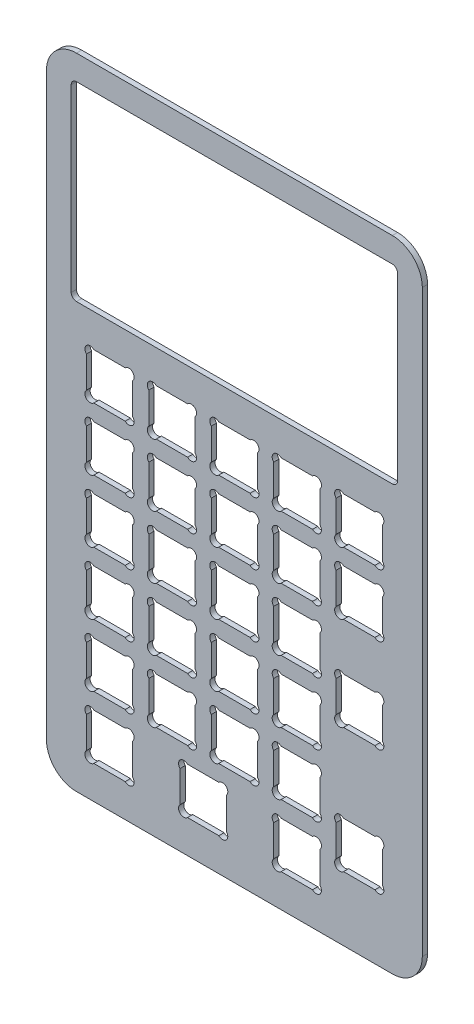
SolidWorks part; units mm, degrees
material "Brass"
ref_plane "Front Plane" through (0, 0, 0) normal (0, 0, 1) x (1, 0, 0)
ref_plane "Top Plane" through (0, 0, 0) normal (0, 1, 0) x (1, 0, 0)
ref_plane "Right Plane" through (0, 0, 0) normal (1, 0, 0) x (0, 0, -1)
sketch "Sketch1" plane through (0, 0, 0) normal (0, 0, 1) x (1, 0, 0)
  line L0 (-80.6226, 118.5954) -> (-71.1174, 118.5954)
  line L1 (0, 0) -> (-113.9, 0)
  line L2 (0, 0) -> (0, 193.7954)
  line L3 (0, 193.7954) -> (-113.9, 193.7954)
  line L4 (-113.9, 0) -> (-113.9, 193.7954)
  line L5 (-99.5426, 118.5954) -> (-90.0374, 118.5954)
  line L6 (-101.7877, 116.3503) -> (-101.7877, 106.8451)
  line L7 (-99.5426, 104.6) -> (-90.0374, 104.6)
  line L8 (-87.7923, 116.3503) -> (-87.7923, 106.8451)
  line L9 (-82.8677, 116.3503) -> (-82.8677, 106.8451)
  line L10 (-80.6226, 104.6) -> (-71.1174, 104.6)
  line L11 (-68.8723, 116.3503) -> (-68.8723, 106.8451)
  line L12 (-61.7026, 118.5954) -> (-52.1974, 118.5954)
  line L13 (-63.9477, 116.3503) -> (-63.9477, 106.8451)
  line L14 (-61.7026, 104.6) -> (-52.1974, 104.6)
  line L15 (-49.9523, 116.3503) -> (-49.9523, 106.8451)
  line L16 (-42.7826, 118.5954) -> (-33.2774, 118.5954)
  line L17 (-45.0277, 116.3503) -> (-45.0277, 106.8451)
  line L18 (-42.7826, 104.6) -> (-33.2774, 104.6)
  line L19 (-31.0323, 116.3503) -> (-31.0323, 106.8451)
  line L20 (-23.8626, 118.5954) -> (-14.3574, 118.5954)
  line L21 (-26.1077, 116.3503) -> (-26.1077, 106.8451)
  line L22 (-23.8626, 104.6) -> (-14.3574, 104.6)
  line L23 (-12.1123, 116.3503) -> (-12.1123, 106.8451)
  line L24 (-80.6226, 99.6754) -> (-71.1174, 99.6754)
  line L25 (-82.8677, 97.4303) -> (-82.8677, 87.9251)
  line L26 (-80.6226, 85.68) -> (-71.1174, 85.68)
  line L27 (-68.8723, 97.4303) -> (-68.8723, 87.9251)
  line L28 (-61.7026, 99.6754) -> (-52.1974, 99.6754)
  line L29 (-63.9477, 97.4303) -> (-63.9477, 87.9251)
  line L30 (-61.7026, 85.68) -> (-52.1974, 85.68)
  line L31 (-49.9523, 97.4303) -> (-49.9523, 87.9251)
  line L32 (-42.7826, 99.6754) -> (-33.2774, 99.6754)
  line L33 (-45.0277, 97.4303) -> (-45.0277, 87.9251)
  line L34 (-42.7826, 85.68) -> (-33.2774, 85.68)
  line L35 (-31.0323, 97.4303) -> (-31.0323, 87.9251)
  line L36 (-23.8626, 99.6754) -> (-14.3574, 99.6754)
  line L37 (-26.1077, 97.4303) -> (-26.1077, 87.9251)
  line L38 (-23.8626, 85.68) -> (-14.3574, 85.68)
  line L39 (-12.1123, 97.4303) -> (-12.1123, 87.9251)
  line L40 (-80.6226, 80.7554) -> (-71.1174, 80.7554)
  line L41 (-82.8677, 78.5103) -> (-82.8677, 69.0051)
  line L42 (-80.6226, 66.76) -> (-71.1174, 66.76)
  line L43 (-68.8723, 78.5103) -> (-68.8723, 69.0051)
  line L44 (-61.7026, 80.7554) -> (-52.1974, 80.7554)
  line L45 (-63.9477, 78.5103) -> (-63.9477, 69.0051)
  line L46 (-61.7026, 66.76) -> (-52.1974, 66.76)
  line L47 (-49.9523, 78.5103) -> (-49.9523, 69.0051)
  line L48 (-42.7826, 80.7554) -> (-33.2774, 80.7554)
  line L49 (-45.0277, 78.5103) -> (-45.0277, 69.0051)
  line L50 (-42.7826, 66.76) -> (-33.2774, 66.76)
  line L51 (-31.0323, 78.5103) -> (-31.0323, 69.0051)
  line L56 (-80.6226, 61.8354) -> (-71.1174, 61.8354)
  line L57 (-82.8677, 59.5903) -> (-82.8677, 50.0851)
  line L58 (-80.6226, 47.84) -> (-71.1174, 47.84)
  line L59 (-68.8723, 59.5903) -> (-68.8723, 50.0851)
  line L60 (-61.7026, 61.8354) -> (-52.1974, 61.8354)
  line L61 (-63.9477, 59.5903) -> (-63.9477, 50.0851)
  line L62 (-61.7026, 47.84) -> (-52.1974, 47.84)
  line L63 (-49.9523, 59.5903) -> (-49.9523, 50.0851)
  line L64 (-42.7826, 61.8354) -> (-33.2774, 61.8354)
  line L65 (-45.0277, 59.5903) -> (-45.0277, 50.0851)
  line L66 (-42.7826, 47.84) -> (-33.2774, 47.84)
  line L67 (-31.0323, 59.5903) -> (-31.0323, 50.0851)
  line L72 (-80.6226, 42.9154) -> (-71.1174, 42.9154)
  line L73 (-82.8677, 40.6703) -> (-82.8677, 31.1651)
  line L74 (-80.6226, 28.92) -> (-71.1174, 28.92)
  line L75 (-68.8723, 40.6703) -> (-68.8723, 31.1651)
  line L76 (-61.7026, 42.9154) -> (-52.1974, 42.9154)
  line L77 (-63.9477, 40.6703) -> (-63.9477, 31.1651)
  line L78 (-61.7026, 28.92) -> (-52.1974, 28.92)
  line L79 (-49.9523, 40.6703) -> (-49.9523, 31.1651)
  line L80 (-42.7826, 42.9154) -> (-33.2774, 42.9154)
  line L81 (-45.0277, 40.6703) -> (-45.0277, 31.1651)
  line L82 (-42.7826, 28.92) -> (-33.2774, 28.92)
  line L83 (-31.0323, 40.6703) -> (-31.0323, 31.1651)
  line L96 (-42.7826, 23.9954) -> (-33.2774, 23.9954)
  line L97 (-45.0277, 21.7503) -> (-45.0277, 12.2451)
  line L98 (-42.7826, 10) -> (-33.2774, 10)
  line L99 (-31.0323, 21.7503) -> (-31.0323, 12.2451)
  line L104 (-99.5426, 99.6754) -> (-90.0374, 99.6754)
  line L105 (-101.7877, 97.4303) -> (-101.7877, 87.9251)
  line L106 (-99.5426, 85.68) -> (-90.0374, 85.68)
  line L107 (-87.7923, 97.4303) -> (-87.7923, 87.9251)
  line L108 (-99.5426, 80.7554) -> (-90.0374, 80.7554)
  line L109 (-101.7877, 78.5103) -> (-101.7877, 69.0051)
  line L110 (-99.5426, 66.76) -> (-90.0374, 66.76)
  line L111 (-87.7923, 78.5103) -> (-87.7923, 69.0051)
  line L112 (-99.5426, 61.8354) -> (-90.0374, 61.8354)
  line L113 (-101.7877, 59.5903) -> (-101.7877, 50.0851)
  line L114 (-99.5426, 47.84) -> (-90.0374, 47.84)
  line L115 (-87.7923, 59.5903) -> (-87.7923, 50.0851)
  line L116 (-99.5426, 42.9154) -> (-90.0374, 42.9154)
  line L117 (-101.7877, 40.6703) -> (-101.7877, 31.1651)
  line L118 (-99.5426, 28.92) -> (-90.0374, 28.92)
  line L119 (-87.7923, 40.6703) -> (-87.7923, 31.1651)
  line L120 (-99.5426, 23.9954) -> (-90.0374, 23.9954)
  line L121 (-101.7877, 21.7503) -> (-101.7877, 12.2451)
  line L122 (-99.5426, 10) -> (-90.0374, 10)
  line L123 (-87.7923, 21.7503) -> (-87.7923, 12.2451)
  line L124 (-23.8626, 80.7554) -> (-14.3574, 80.7554) [skipped]
  line L125 (-26.1077, 78.5103) -> (-26.1077, 69.0051) [skipped]
  line L126 (-23.8626, 66.76) -> (-14.3574, 66.76) [skipped]
  line L127 (-12.1123, 78.5103) -> (-12.1123, 69.0051) [skipped]
  line L128 (-23.8626, 61.8354) -> (-14.3574, 61.8354) [skipped]
  line L129 (-26.1077, 59.5903) -> (-26.1077, 50.0851) [skipped]
  line L130 (-23.8626, 47.84) -> (-14.3574, 47.84) [skipped]
  line L131 (-12.1123, 59.5903) -> (-12.1123, 50.0851) [skipped]
  line L132 (-23.8626, 42.9154) -> (-14.3574, 42.9154) [skipped]
  line L133 (-26.1077, 40.6703) -> (-26.1077, 31.1651) [skipped]
  line L134 (-23.8626, 28.92) -> (-14.3574, 28.92) [skipped]
  line L135 (-12.1123, 40.6703) -> (-12.1123, 31.1651) [skipped]
  line L136 (-23.8626, 23.9954) -> (-14.3574, 23.9954) [skipped]
  line L137 (-26.1077, 21.7503) -> (-26.1077, 12.2451) [skipped]
  line L138 (-23.8626, 10) -> (-14.3574, 10) [skipped]
  line L139 (-12.1123, 21.7503) -> (-12.1123, 12.2451) [skipped]
  line L140 (-80.6226, 23.9954) -> (-71.1174, 23.9954) [skipped]
  line L141 (-82.8677, 21.7503) -> (-82.8677, 12.2451) [skipped]
  line L142 (-80.6226, 10) -> (-71.1174, 10) [skipped]
  line L143 (-68.8723, 21.7503) -> (-68.8723, 12.2451) [skipped]
  line L144 (-61.7026, 23.9954) -> (-52.1974, 23.9954) [skipped]
  line L145 (-63.9477, 21.7503) -> (-63.9477, 12.2451) [skipped]
  line L146 (-61.7026, 10) -> (-52.1974, 10) [skipped]
  line L147 (-49.9523, 21.7503) -> (-49.9523, 12.2451) [skipped]
  line L148 (-68.8723, 31.1651) -> (-63.9477, 31.1651) construction
  line L149 (-71.1626, 23.9954) -> (-61.6574, 23.9954)
  line L150 (-73.4077, 21.7503) -> (-73.4077, 12.2451)
  line L151 (-71.1626, 10) -> (-61.6574, 10)
  line L152 (-59.4123, 21.7503) -> (-59.4123, 12.2451)
  line L153 (-23.8626, 33.4554) -> (-14.3574, 33.4554)
  line L154 (-26.1077, 31.2103) -> (-26.1077, 21.7051)
  line L155 (-23.8626, 19.46) -> (-14.3574, 19.46)
  line L156 (-12.1123, 31.2103) -> (-12.1123, 21.7051)
  line L157 (-23.8626, 71.2954) -> (-14.3574, 71.2954)
  line L158 (-26.1077, 69.0503) -> (-26.1077, 59.5451)
  line L159 (-23.8626, 57.3) -> (-14.3574, 57.3)
  line L160 (-12.1123, 69.0503) -> (-12.1123, 59.5451)
  line L161 (-33.2774, 28.92) -> (-33.2774, 23.9954) construction
  line L162 (-33.2774, 66.76) -> (-33.2774, 61.8354) construction
  line L163 (-56.95, 193.7954) -> (-56.95, 0) construction
  line L164 (-104.8125, 186.2954) -> (-9.0875, 186.2954)
  line L165 (-106.4, 184.7079) -> (-106.4, 130.1829)
  line L166 (-104.8125, 128.5954) -> (-9.0875, 128.5954)
  line L167 (-7.5, 184.7079) -> (-7.5, 130.1829)
  arc A4 (-99.5426, 118.5954) -> (-101.7877, 116.3503) centre (-100.6652, 117.4729) ccw
  arc A5 (-101.7877, 106.8451) -> (-99.5426, 104.6) centre (-100.6652, 105.7225) ccw
  arc A6 (-90.0374, 104.6) -> (-87.7923, 106.8451) centre (-88.9148, 105.7225) ccw
  arc A7 (-87.7923, 116.3503) -> (-90.0374, 118.5954) centre (-88.9148, 117.4729) ccw
  arc A8 (-80.6226, 118.5954) -> (-82.8677, 116.3503) centre (-81.7452, 117.4729) ccw
  arc A9 (-82.8677, 106.8451) -> (-80.6226, 104.6) centre (-81.7452, 105.7225) ccw
  arc A10 (-71.1174, 104.6) -> (-68.8723, 106.8451) centre (-69.9948, 105.7225) ccw
  arc A11 (-68.8723, 116.3503) -> (-71.1174, 118.5954) centre (-69.9948, 117.4729) ccw
  arc A12 (-61.7026, 118.5954) -> (-63.9477, 116.3503) centre (-62.8252, 117.4729) ccw
  arc A13 (-63.9477, 106.8451) -> (-61.7026, 104.6) centre (-62.8252, 105.7225) ccw
  arc A14 (-52.1974, 104.6) -> (-49.9523, 106.8451) centre (-51.0748, 105.7225) ccw
  arc A15 (-49.9523, 116.3503) -> (-52.1974, 118.5954) centre (-51.0748, 117.4729) ccw
  arc A16 (-42.7826, 118.5954) -> (-45.0277, 116.3503) centre (-43.9052, 117.4729) ccw
  arc A17 (-45.0277, 106.8451) -> (-42.7826, 104.6) centre (-43.9052, 105.7225) ccw
  arc A18 (-33.2774, 104.6) -> (-31.0323, 106.8451) centre (-32.1548, 105.7225) ccw
  arc A19 (-31.0323, 116.3503) -> (-33.2774, 118.5954) centre (-32.1548, 117.4729) ccw
  arc A20 (-23.8626, 118.5954) -> (-26.1077, 116.3503) centre (-24.9852, 117.4729) ccw
  arc A21 (-26.1077, 106.8451) -> (-23.8626, 104.6) centre (-24.9852, 105.7225) ccw
  arc A22 (-14.3574, 104.6) -> (-12.1123, 106.8451) centre (-13.2348, 105.7225) ccw
  arc A23 (-12.1123, 116.3503) -> (-14.3574, 118.5954) centre (-13.2348, 117.4729) ccw
  arc A24 (-80.6226, 99.6754) -> (-82.8677, 97.4303) centre (-81.7452, 98.5529) ccw
  arc A25 (-82.8677, 87.9251) -> (-80.6226, 85.68) centre (-81.7452, 86.8025) ccw
  arc A26 (-71.1174, 85.68) -> (-68.8723, 87.9251) centre (-69.9948, 86.8025) ccw
  arc A27 (-68.8723, 97.4303) -> (-71.1174, 99.6754) centre (-69.9948, 98.5529) ccw
  arc A28 (-61.7026, 99.6754) -> (-63.9477, 97.4303) centre (-62.8252, 98.5529) ccw
  arc A29 (-63.9477, 87.9251) -> (-61.7026, 85.68) centre (-62.8252, 86.8025) ccw
  arc A30 (-52.1974, 85.68) -> (-49.9523, 87.9251) centre (-51.0748, 86.8025) ccw
  arc A31 (-49.9523, 97.4303) -> (-52.1974, 99.6754) centre (-51.0748, 98.5529) ccw
  arc A32 (-42.7826, 99.6754) -> (-45.0277, 97.4303) centre (-43.9052, 98.5529) ccw
  arc A33 (-45.0277, 87.9251) -> (-42.7826, 85.68) centre (-43.9052, 86.8025) ccw
  arc A34 (-33.2774, 85.68) -> (-31.0323, 87.9251) centre (-32.1548, 86.8025) ccw
  arc A35 (-31.0323, 97.4303) -> (-33.2774, 99.6754) centre (-32.1548, 98.5529) ccw
  arc A36 (-23.8626, 99.6754) -> (-26.1077, 97.4303) centre (-24.9852, 98.5529) ccw
  arc A37 (-26.1077, 87.9251) -> (-23.8626, 85.68) centre (-24.9852, 86.8025) ccw
  arc A38 (-14.3574, 85.68) -> (-12.1123, 87.9251) centre (-13.2348, 86.8025) ccw
  arc A39 (-12.1123, 97.4303) -> (-14.3574, 99.6754) centre (-13.2348, 98.5529) ccw
  arc A40 (-80.6226, 80.7554) -> (-82.8677, 78.5103) centre (-81.7452, 79.6329) ccw
  arc A41 (-82.8677, 69.0051) -> (-80.6226, 66.76) centre (-81.7452, 67.8825) ccw
  arc A42 (-71.1174, 66.76) -> (-68.8723, 69.0051) centre (-69.9948, 67.8825) ccw
  arc A43 (-68.8723, 78.5103) -> (-71.1174, 80.7554) centre (-69.9948, 79.6329) ccw
  arc A44 (-61.7026, 80.7554) -> (-63.9477, 78.5103) centre (-62.8252, 79.6329) ccw
  arc A45 (-63.9477, 69.0051) -> (-61.7026, 66.76) centre (-62.8252, 67.8825) ccw
  arc A46 (-52.1974, 66.76) -> (-49.9523, 69.0051) centre (-51.0748, 67.8825) ccw
  arc A47 (-49.9523, 78.5103) -> (-52.1974, 80.7554) centre (-51.0748, 79.6329) ccw
  arc A48 (-42.7826, 80.7554) -> (-45.0277, 78.5103) centre (-43.9052, 79.6329) ccw
  arc A49 (-45.0277, 69.0051) -> (-42.7826, 66.76) centre (-43.9052, 67.8825) ccw
  arc A50 (-33.2774, 66.76) -> (-31.0323, 69.0051) centre (-32.1548, 67.8825) ccw
  arc A51 (-31.0323, 78.5103) -> (-33.2774, 80.7554) centre (-32.1548, 79.6329) ccw
  arc A56 (-80.6226, 61.8354) -> (-82.8677, 59.5903) centre (-81.7452, 60.7129) ccw
  arc A57 (-82.8677, 50.0851) -> (-80.6226, 47.84) centre (-81.7452, 48.9625) ccw
  arc A58 (-71.1174, 47.84) -> (-68.8723, 50.0851) centre (-69.9948, 48.9625) ccw
  arc A59 (-68.8723, 59.5903) -> (-71.1174, 61.8354) centre (-69.9948, 60.7129) ccw
  arc A60 (-61.7026, 61.8354) -> (-63.9477, 59.5903) centre (-62.8252, 60.7129) ccw
  arc A61 (-63.9477, 50.0851) -> (-61.7026, 47.84) centre (-62.8252, 48.9625) ccw
  arc A62 (-52.1974, 47.84) -> (-49.9523, 50.0851) centre (-51.0748, 48.9625) ccw
  arc A63 (-49.9523, 59.5903) -> (-52.1974, 61.8354) centre (-51.0748, 60.7129) ccw
  arc A64 (-42.7826, 61.8354) -> (-45.0277, 59.5903) centre (-43.9052, 60.7129) ccw
  arc A65 (-45.0277, 50.0851) -> (-42.7826, 47.84) centre (-43.9052, 48.9625) ccw
  arc A66 (-33.2774, 47.84) -> (-31.0323, 50.0851) centre (-32.1548, 48.9625) ccw
  arc A67 (-31.0323, 59.5903) -> (-33.2774, 61.8354) centre (-32.1548, 60.7129) ccw
  arc A72 (-80.6226, 42.9154) -> (-82.8677, 40.6703) centre (-81.7452, 41.7929) ccw
  arc A73 (-82.8677, 31.1651) -> (-80.6226, 28.92) centre (-81.7452, 30.0425) ccw
  arc A74 (-71.1174, 28.92) -> (-68.8723, 31.1651) centre (-69.9948, 30.0425) ccw
  arc A75 (-68.8723, 40.6703) -> (-71.1174, 42.9154) centre (-69.9948, 41.7929) ccw
  arc A76 (-61.7026, 42.9154) -> (-63.9477, 40.6703) centre (-62.8252, 41.7929) ccw
  arc A77 (-63.9477, 31.1651) -> (-61.7026, 28.92) centre (-62.8252, 30.0425) ccw
  arc A78 (-52.1974, 28.92) -> (-49.9523, 31.1651) centre (-51.0748, 30.0425) ccw
  arc A79 (-49.9523, 40.6703) -> (-52.1974, 42.9154) centre (-51.0748, 41.7929) ccw
  arc A80 (-42.7826, 42.9154) -> (-45.0277, 40.6703) centre (-43.9052, 41.7929) ccw
  arc A81 (-45.0277, 31.1651) -> (-42.7826, 28.92) centre (-43.9052, 30.0425) ccw
  arc A82 (-33.2774, 28.92) -> (-31.0323, 31.1651) centre (-32.1548, 30.0425) ccw
  arc A83 (-31.0323, 40.6703) -> (-33.2774, 42.9154) centre (-32.1548, 41.7929) ccw
  arc A96 (-42.7826, 23.9954) -> (-45.0277, 21.7503) centre (-43.9052, 22.8729) ccw
  arc A97 (-45.0277, 12.2451) -> (-42.7826, 10) centre (-43.9052, 11.1225) ccw
  arc A98 (-33.2774, 10) -> (-31.0323, 12.2451) centre (-32.1548, 11.1225) ccw
  arc A99 (-31.0323, 21.7503) -> (-33.2774, 23.9954) centre (-32.1548, 22.8729) ccw
  arc A104 (-99.5426, 99.6754) -> (-101.7877, 97.4303) centre (-100.6652, 98.5529) ccw
  arc A105 (-101.7877, 87.9251) -> (-99.5426, 85.68) centre (-100.6652, 86.8025) ccw
  arc A106 (-90.0374, 85.68) -> (-87.7923, 87.9251) centre (-88.9148, 86.8025) ccw
  arc A107 (-87.7923, 97.4303) -> (-90.0374, 99.6754) centre (-88.9148, 98.5529) ccw
  arc A108 (-99.5426, 80.7554) -> (-101.7877, 78.5103) centre (-100.6652, 79.6329) ccw
  arc A109 (-101.7877, 69.0051) -> (-99.5426, 66.76) centre (-100.6652, 67.8825) ccw
  arc A110 (-90.0374, 66.76) -> (-87.7923, 69.0051) centre (-88.9148, 67.8825) ccw
  arc A111 (-87.7923, 78.5103) -> (-90.0374, 80.7554) centre (-88.9148, 79.6329) ccw
  arc A112 (-99.5426, 61.8354) -> (-101.7877, 59.5903) centre (-100.6652, 60.7129) ccw
  arc A113 (-101.7877, 50.0851) -> (-99.5426, 47.84) centre (-100.6652, 48.9625) ccw
  arc A114 (-90.0374, 47.84) -> (-87.7923, 50.0851) centre (-88.9148, 48.9625) ccw
  arc A115 (-87.7923, 59.5903) -> (-90.0374, 61.8354) centre (-88.9148, 60.7129) ccw
  arc A116 (-99.5426, 42.9154) -> (-101.7877, 40.6703) centre (-100.6652, 41.7929) ccw
  arc A117 (-101.7877, 31.1651) -> (-99.5426, 28.92) centre (-100.6652, 30.0425) ccw
  arc A118 (-90.0374, 28.92) -> (-87.7923, 31.1651) centre (-88.9148, 30.0425) ccw
  arc A119 (-87.7923, 40.6703) -> (-90.0374, 42.9154) centre (-88.9148, 41.7929) ccw
  arc A120 (-99.5426, 23.9954) -> (-101.7877, 21.7503) centre (-100.6652, 22.8729) ccw
  arc A121 (-101.7877, 12.2451) -> (-99.5426, 10) centre (-100.6652, 11.1225) ccw
  arc A122 (-90.0374, 10) -> (-87.7923, 12.2451) centre (-88.9148, 11.1225) ccw
  arc A123 (-87.7923, 21.7503) -> (-90.0374, 23.9954) centre (-88.9148, 22.8729) ccw
  arc A124 (-23.8626, 80.7554) -> (-26.1077, 78.5103) centre (-24.9852, 79.6329) ccw [skipped]
  arc A125 (-26.1077, 69.0051) -> (-23.8626, 66.76) centre (-24.9852, 67.8825) ccw [skipped]
  arc A126 (-14.3574, 66.76) -> (-12.1123, 69.0051) centre (-13.2348, 67.8825) ccw [skipped]
  arc A127 (-12.1123, 78.5103) -> (-14.3574, 80.7554) centre (-13.2348, 79.6329) ccw [skipped]
  arc A128 (-23.8626, 61.8354) -> (-26.1077, 59.5903) centre (-24.9852, 60.7129) ccw [skipped]
  arc A129 (-26.1077, 50.0851) -> (-23.8626, 47.84) centre (-24.9852, 48.9625) ccw [skipped]
  arc A130 (-14.3574, 47.84) -> (-12.1123, 50.0851) centre (-13.2348, 48.9625) ccw [skipped]
  arc A131 (-12.1123, 59.5903) -> (-14.3574, 61.8354) centre (-13.2348, 60.7129) ccw [skipped]
  arc A132 (-23.8626, 42.9154) -> (-26.1077, 40.6703) centre (-24.9852, 41.7929) ccw [skipped]
  arc A133 (-26.1077, 31.1651) -> (-23.8626, 28.92) centre (-24.9852, 30.0425) ccw [skipped]
  arc A134 (-14.3574, 28.92) -> (-12.1123, 31.1651) centre (-13.2348, 30.0425) ccw [skipped]
  arc A135 (-12.1123, 40.6703) -> (-14.3574, 42.9154) centre (-13.2348, 41.7929) ccw [skipped]
  arc A136 (-23.8626, 23.9954) -> (-26.1077, 21.7503) centre (-24.9852, 22.8729) ccw [skipped]
  arc A137 (-26.1077, 12.2451) -> (-23.8626, 10) centre (-24.9852, 11.1225) ccw [skipped]
  arc A138 (-14.3574, 10) -> (-12.1123, 12.2451) centre (-13.2348, 11.1225) ccw [skipped]
  arc A139 (-12.1123, 21.7503) -> (-14.3574, 23.9954) centre (-13.2348, 22.8729) ccw [skipped]
  arc A140 (-80.6226, 23.9954) -> (-82.8677, 21.7503) centre (-81.7452, 22.8729) ccw [skipped]
  arc A141 (-82.8677, 12.2451) -> (-80.6226, 10) centre (-81.7452, 11.1225) ccw [skipped]
  arc A142 (-71.1174, 10) -> (-68.8723, 12.2451) centre (-69.9948, 11.1225) ccw [skipped]
  arc A143 (-68.8723, 21.7503) -> (-71.1174, 23.9954) centre (-69.9948, 22.8729) ccw [skipped]
  arc A144 (-61.7026, 23.9954) -> (-63.9477, 21.7503) centre (-62.8252, 22.8729) ccw [skipped]
  arc A145 (-63.9477, 12.2451) -> (-61.7026, 10) centre (-62.8252, 11.1225) ccw [skipped]
  arc A146 (-52.1974, 10) -> (-49.9523, 12.2451) centre (-51.0748, 11.1225) ccw [skipped]
  arc A147 (-49.9523, 21.7503) -> (-52.1974, 23.9954) centre (-51.0748, 22.8729) ccw [skipped]
  arc A148 (-71.1626, 23.9954) -> (-73.4077, 21.7503) centre (-72.2852, 22.8729) ccw
  arc A149 (-73.4077, 12.2451) -> (-71.1626, 10) centre (-72.2852, 11.1225) ccw
  arc A150 (-61.6574, 10) -> (-59.4123, 12.2451) centre (-60.5348, 11.1225) ccw
  arc A151 (-59.4123, 21.7503) -> (-61.6574, 23.9954) centre (-60.5348, 22.8729) ccw
  arc A152 (-23.8626, 33.4554) -> (-26.1077, 31.2103) centre (-24.9852, 32.3329) ccw
  arc A153 (-26.1077, 21.7051) -> (-23.8626, 19.46) centre (-24.9852, 20.5825) ccw
  arc A154 (-14.3574, 19.46) -> (-12.1123, 21.7051) centre (-13.2348, 20.5825) ccw
  arc A155 (-12.1123, 31.2103) -> (-14.3574, 33.4554) centre (-13.2348, 32.3329) ccw
  arc A156 (-23.8626, 71.2954) -> (-26.1077, 69.0503) centre (-24.9852, 70.1729) ccw
  arc A157 (-26.1077, 59.5451) -> (-23.8626, 57.3) centre (-24.9852, 58.4225) ccw
  arc A158 (-14.3574, 57.3) -> (-12.1123, 59.5451) centre (-13.2348, 58.4225) ccw
  arc A159 (-12.1123, 69.0503) -> (-14.3574, 71.2954) centre (-13.2348, 70.1729) ccw
  arc A160 (-9.0875, 186.2954) -> (-7.5, 184.7079) centre (-9.0875, 184.7079) cw
  arc A161 (-9.0875, 128.5954) -> (-7.5, 130.1829) centre (-9.0875, 130.1829) ccw
  arc A162 (-106.4, 130.1829) -> (-104.8125, 128.5954) centre (-104.8125, 130.1829) ccw
  arc A163 (-104.8125, 186.2954) -> (-106.4, 184.7079) centre (-104.8125, 184.7079) ccw
  point P8 (-101.7877, 118.5954)
  point P16 (-87.7923, 118.5954)
  point P25 (-101.7877, 104.6)
  point P27 (-87.7923, 104.6)
  point P32 (-26.1077, 26.4577)
  point P155 (-33.2774, 26.4577)
  point P159 (-73.4077, 23.9954)
  point P191 (-56.95, 186.2954)
  point P203 (-59.4123, 23.9954)
  point P206 (-73.4077, 10)
  point P207 (-59.4123, 10)
  point P210 (-66.41, 23.9954)
  point P211 (-66.41, 31.1651)
  point P251 (-26.1077, 33.4554)
  point P259 (-12.1123, 33.4554)
  point P262 (-26.1077, 19.46)
  point P263 (-12.1123, 19.46)
  point P267 (-26.1077, 71.2954)
  point P275 (-12.1123, 71.2954)
  point P278 (-26.1077, 57.3)
  point P282 (-33.2774, 64.2977)
  point P283 (-26.1077, 64.2977)
  point P284 (-7.5, 186.2954)
  point P300 (-7.5, 128.5954)
  point P302 (-56.95, 118.5954)
  point P303 (-56.95, 193.7954)
  point P309 (-106.4, 186.2954)
  point P493 (0, 0)
  dimension "D2" = 1.5875
  dimension "D11" = 7.5
  dimension "D12" = 10
  dimension "D13" = 1.5875
  dimension "D1" = 13.9954
  dimension "D3" = 10
  dimension "D4" = 113.9
  dimension "D5" = 98.9
  dimension "D6" = 57.7
  dimension "D9" = 18.92
  dimension "D10" = 18.92
  dimension "D7" = 5
  dimension "D8" = 6
extrude "Boss-Extrude1" add sketch "Sketch1" along normal blind 1.5875
fillet "Fillet1" radius 9.0875 4 edges at (-113.9, 0, 0.7937) (0, 0, 0.7937) (0, 193.7954, 0.7937) (-113.9, 193.7954, 0.7937)
sketch "Sketch2" plane through (0, 0, 1.5875) normal (0, 0, 1) x (1, 0, 0)
  line L0 (-56.9104, 20.4879) -> (-59.4123, 20.4879)
  line L1 (-73.4077, 13.6456) -> (-72.8578, 13.6456)
  line L2 (-73.4077, 21.7503) -> (-73.4077, 12.2451) construction
  line L3 (-72.8578, 13.6456) -> (-72.8578, 12.3923)
  line L4 (-72.8578, 12.3923) -> (-75.7239, 12.3923)
  line L5 (-75.7239, 12.3923) -> (-75.7239, 10.0423)
  line L6 (-75.7239, 10.0423) -> (-78.7719, 10.0423)
  line L7 (-78.7719, 10.0423) -> (-78.7719, 12.3923)
  line L8 (-78.7719, 12.3923) -> (-82.5644, 12.3923)
  line L9 (-82.5644, 12.3923) -> (-82.5644, 17.4839)
  line L10 (-82.5644, 17.4839) -> (-81.5136, 17.4839)
  line L11 (-81.5136, 17.4839) -> (-81.5136, 20.813)
  line L12 (-81.5136, 20.813) -> (-82.5644, 20.813)
  line L13 (-82.5644, 20.813) -> (-82.5644, 21.3007)
  line L14 (-82.5644, 21.3007) -> (-75.9096, 21.3007)
  line L15 (-75.9096, 21.3007) -> (-75.9096, 20.4879)
  line L16 (-75.9096, 20.4879) -> (-73.4077, 20.4879)
  line L17 (-66.41, 23.9954) -> (-66.41, 10) construction
  line L18 (-61.6574, 23.9954) -> (-71.1626, 23.9954) construction
  line L19 (-71.1626, 10) -> (-61.6574, 10) construction
  line L20 (-56.9104, 21.3007) -> (-56.9104, 20.4879)
  line L21 (-50.2556, 21.3007) -> (-56.9104, 21.3007)
  line L22 (-50.2556, 20.813) -> (-50.2556, 21.3007)
  line L23 (-51.3064, 20.813) -> (-50.2556, 20.813)
  line L24 (-51.3064, 17.4839) -> (-51.3064, 20.813)
  line L25 (-50.2556, 17.4839) -> (-51.3064, 17.4839)
  line L26 (-50.2556, 12.3923) -> (-50.2556, 17.4839)
  line L27 (-54.0481, 12.3923) -> (-50.2556, 12.3923)
  line L28 (-54.0481, 10.0423) -> (-54.0481, 12.3923)
  line L29 (-57.0961, 10.0423) -> (-54.0481, 10.0423)
  line L30 (-57.0961, 12.3923) -> (-57.0961, 10.0423)
  line L31 (-59.9622, 12.3923) -> (-57.0961, 12.3923)
  line L32 (-59.9622, 13.6456) -> (-59.9622, 12.3923)
  line L33 (-59.4123, 13.6456) -> (-59.9622, 13.6456)
  point P26 (-81.4923, 16.9299)
  dimension "D1" = 6.6548
  dimension "D2" = 3.048
  dimension "D3" = 32.3088
  dimension "D4" = 0.8128
